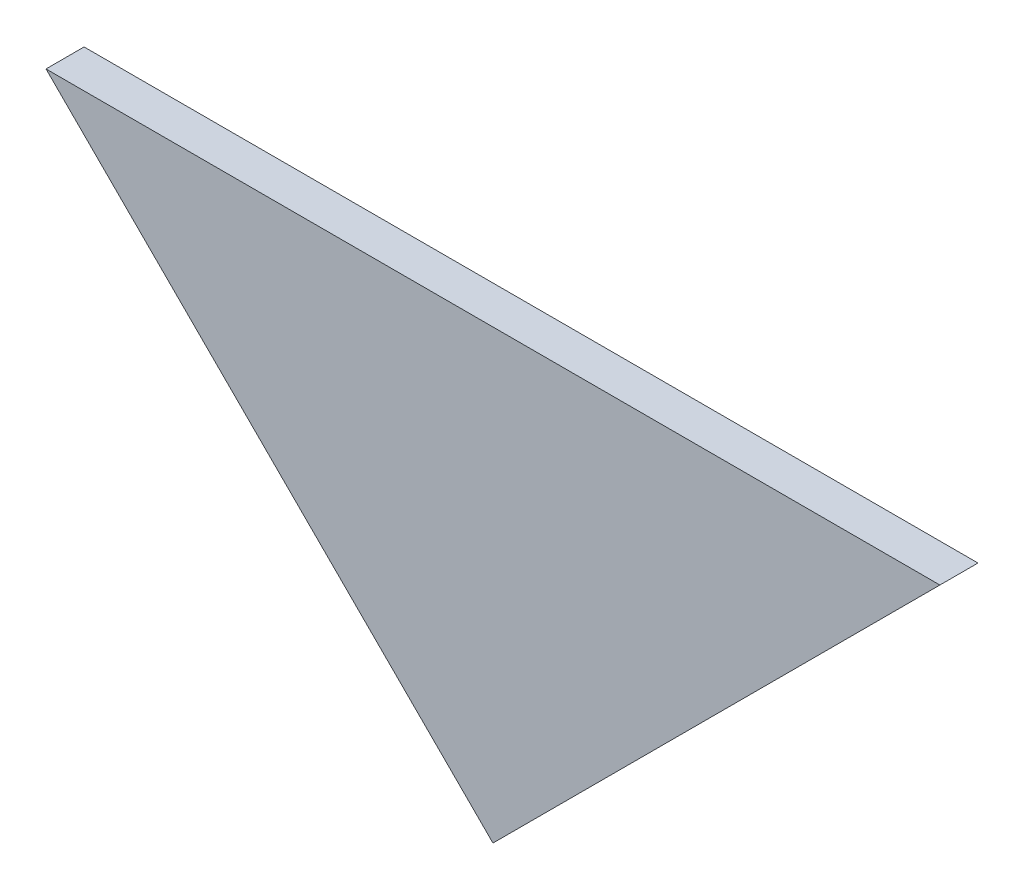
SolidWorks part; units mm, degrees
material "Pine"
ref_plane "Front Plane" through (0, 0, 0) normal (0, 0, 1) x (1, 0, 0)
ref_plane "Top Plane" through (0, 0, 0) normal (0, 1, 0) x (1, 0, 0)
ref_plane "Right Plane" through (0, 0, 0) normal (1, 0, 0) x (0, 0, -1)
sketch "Sketch1" plane through (0, 0, 0) normal (0, 0, 1) x (1, 0, 0)
  line L3 (172.1892, 37.4911) -> (-107.2108, 37.4911) construction
  line L4 (-107.2108, 37.4911) -> (32.4892, -102.2089)
  line L5 (32.4892, -102.2089) -> (172.1892, 37.4911)
  line L6 (172.1892, 37.4911) -> (-107.2108, 37.4911)
  circle A0 centre (32.4892, -66.2878) radius 3.175 construction
  circle A1 centre (110.8682, 12.0911) radius 3.175 construction
  circle A2 centre (-45.8898, 12.0911) radius 3.175 construction
  dimension "D4" = 6.35
  dimension "D5" = 25.4
  dimension "D6" = 25.4
  dimension "D7" = 25.4
  dimension "D8" = 25.4
  dimension "D9" = 25.4
  dimension "D10" = 25.4
  dimension "D1" = 279.4
  dimension "D2" = 45
  dimension "D3" = 90
extrude "Boss-Extrude1" add sketch "Sketch1" along normal blind 11.9062
